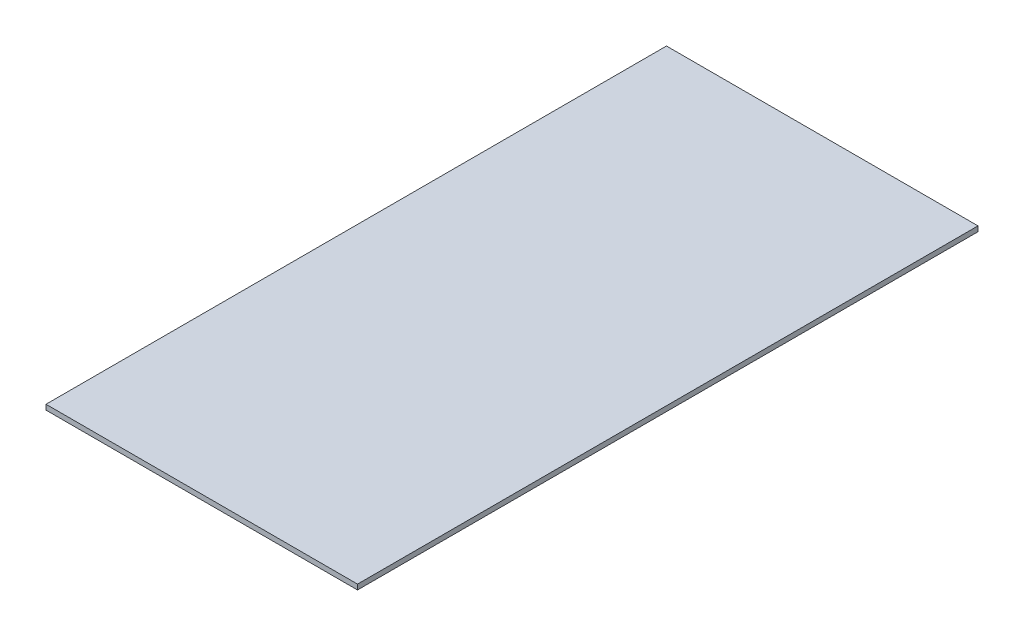
SolidWorks part; units mm, degrees
ref_plane "前视" through (0, 0, 0) normal (0, 0, 1) x (1, 0, 0)
ref_plane "上视" through (0, 0, 0) normal (0, 1, 0) x (1, 0, 0)
ref_plane "右视" through (0, 0, 0) normal (1, 0, 0) x (0, 0, -1)
sketch "草图1" plane through (0, 0, 0) normal (0, 1, 0) x (1, 0, 0)
  line L0 (0, -1215) -> (1220, -1215) construction
  line L1 (0, 0) -> (1220, 0)
  line L2 (0, 0) -> (0, -2430)
  line L3 (0, -2430) -> (1220, -2430)
  line L4 (1220, 0) -> (1220, -2430)
  dimension "D1" = 1220
extrude "凸台-拉伸1" add sketch "草图1" against normal blind 20
